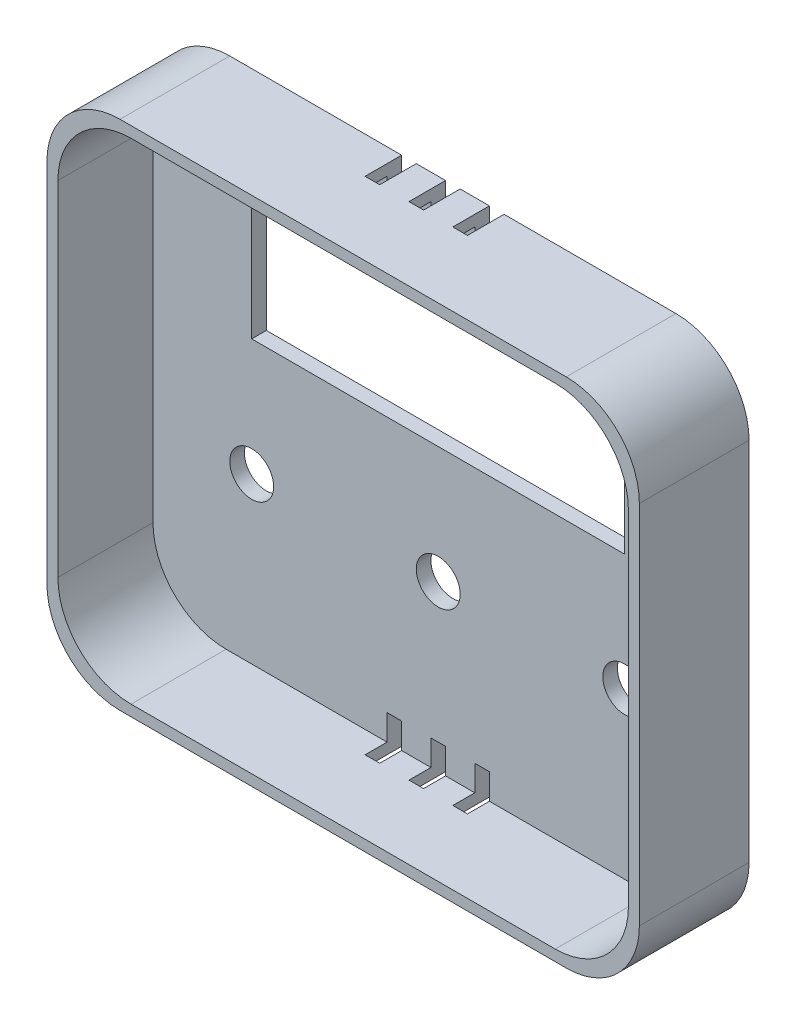
SolidWorks part; units mm, degrees
ref_plane "Plan de face" through (0, 0, 0) normal (0, 0, 1) x (1, 0, 0)
ref_plane "Plan de dessus" through (0, 0, 0) normal (0, 1, 0) x (1, 0, 0)
ref_plane "Plan de droite" through (0, 0, 0) normal (1, 0, 0) x (0, 0, -1)
sketch "Esquisse1" plane through (0, 0, 0) normal (0, 0, 1) x (1, 0, 0)
  line L1 (0, 0) -> (51, 0)
  line L2 (0, 0) -> (0, 19.5)
  line L3 (0, 19.5) -> (51, 19.5)
  line L4 (51, 0) -> (51, 19.5)
  line L5 (-5, 30) -> (56, 30)
  line L6 (-15, 20) -> (-15, -30)
  line L7 (-5, -40) -> (56, -40)
  line L8 (66, 20) -> (66, -30)
  circle A0 centre (0, -16) radius 3
  circle A1 centre (25.5, -16) radius 3
  circle A2 centre (51, -16) radius 3
  arc A3 (56, -40) -> (66, -30) centre (56, -30) ccw
  arc A4 (-15, -30) -> (-5, -40) centre (-5, -30) ccw
  arc A5 (-5, 30) -> (-15, 20) centre (-5, 20) ccw
  arc A6 (56, 30) -> (66, 20) centre (56, 20) cw
  dimension "D1" = 10
extrude "Boss.-Extru.1" add sketch "Esquisse1" along normal blind 2
sketch "Esquisse2" plane through (0, 0, 2) normal (0, 0, 1) x (1, 0, 0)
  line L0 (-13.5, 18.5) -> (-13.5, -28.5)
  line L1 (-5, 30) -> (56, 30)
  line L2 (-15, 20) -> (-15, -30)
  line L3 (-5, -40) -> (56, -40)
  line L4 (66, 20) -> (66, -30)
  line L5 (-3.5, -38.5) -> (54.5, -38.5)
  line L6 (64.5, 18.5) -> (64.5, -28.5)
  line L7 (-3.5, 28.5) -> (54.5, 28.5)
  line L8 (-15, 30) -> (-15, -40) construction
  line L9 (-15, -40) -> (66, -40) construction
  line L10 (-13.5, 28.5) -> (-13.5, -38.5) construction
  line L11 (-13.5, -38.5) -> (64.5, -38.5) construction
  line L12 (66, 30) -> (66, -40) construction
  line L13 (64.5, 28.5) -> (64.5, -38.5) construction
  line L14 (-15, 30) -> (66, 30) construction
  line L15 (-13.5, 28.5) -> (64.5, 28.5) construction
  arc A0 (-15, -30) -> (-5, -40) centre (-5, -30) ccw
  arc A1 (-13.5, -28.5) -> (-3.5, -38.5) centre (-3.5, -28.5) ccw
  arc A2 (56, -40) -> (66, -30) centre (56, -30) ccw
  arc A3 (54.5, -38.5) -> (64.5, -28.5) centre (54.5, -28.5) ccw
  arc A4 (56, 30) -> (66, 20) centre (56, 20) cw
  arc A5 (64.5, 18.5) -> (54.5, 28.5) centre (54.5, 18.5) ccw
  arc A6 (-5, 30) -> (-15, 20) centre (-5, 20) ccw
  arc A7 (-13.5, 18.5) -> (-3.5, 28.5) centre (-3.5, 18.5) cw
  dimension "D2" = 10
  dimension "D1" = 1.5
extrude "Boss.-Extru.2" add sketch "Esquisse2" along normal blind 13
sketch "Esquisse3" plane through (0, 0, 0) normal (0, 0, -1) x (-1, 0, 0)
  line L0 (-24.5, 33.6618) -> (-26.5, 33.6618)
  line L1 (-32.5, 33.7159) -> (-30.5, 33.7159)
  line L2 (-32.5, 33.7159) -> (-32.5, 25)
  line L3 (-32.5, 25) -> (-30.5, 25)
  line L4 (-30.5, 33.7159) -> (-30.5, 25)
  line L5 (-24.5, 33.6618) -> (-24.5, 25)
  line L6 (-24.5, 25) -> (-26.5, 25)
  line L7 (-26.5, 33.6618) -> (-26.5, 25)
  line L8 (-20.5, 33.4453) -> (-18.5, 33.4453)
  line L9 (-20.5, 33.4453) -> (-20.5, 25)
  line L10 (-20.5, 25) -> (-18.5, 25)
  line L11 (-18.5, 33.4453) -> (-18.5, 25)
  line L12 (-24.5, -35) -> (-26.5, -35)
  line L13 (-32.5, -35) -> (-30.5, -35)
  line L14 (-32.5, -35) -> (-32.5, -43.4932)
  line L15 (-32.5, -43.4932) -> (-30.5, -43.4932)
  line L16 (-30.5, -35) -> (-30.5, -43.4932)
  line L17 (-24.5, -35) -> (-24.5, -43.4932)
  line L18 (-24.5, -43.4932) -> (-26.5, -43.4932)
  line L19 (-26.5, -35) -> (-26.5, -43.4932)
  line L20 (-20.5, -35) -> (-18.5, -35)
  line L21 (-20.5, -35) -> (-20.5, -43.4932)
  line L22 (-20.5, -43.4932) -> (-18.5, -43.4932)
  line L23 (-18.5, -35) -> (-18.5, -43.4932)
  point P12 (0, 0)
  point P13 (0, 0)
  point P14 (-50.6312, 23.9736)
  point P15 (0, 0)
  point P16 (-7.4401, 23.9736)
  point P17 (0, 0)
  point P18 (0, 0)
  point P19 (0, 0)
  point P20 (0, 0)
  point P21 (0, 0)
  point P22 (0, 0)
  point P23 (0, 0)
  point P24 (0, 0)
  point P25 (0, 0)
  point P38 (0, 0)
  point P39 (0, 0)
  point P40 (0, 0)
  point P41 (0, 0)
  point P42 (0, 0)
  point P43 (0, 0)
  point P44 (0, 0)
  point P45 (0, 0)
  point P46 (0, 0)
  point P47 (0, 0)
  point P48 (0, 0)
extrude "Enlèv. mat.-Extru.1" cut sketch "Esquisse3" against normal blind 5
